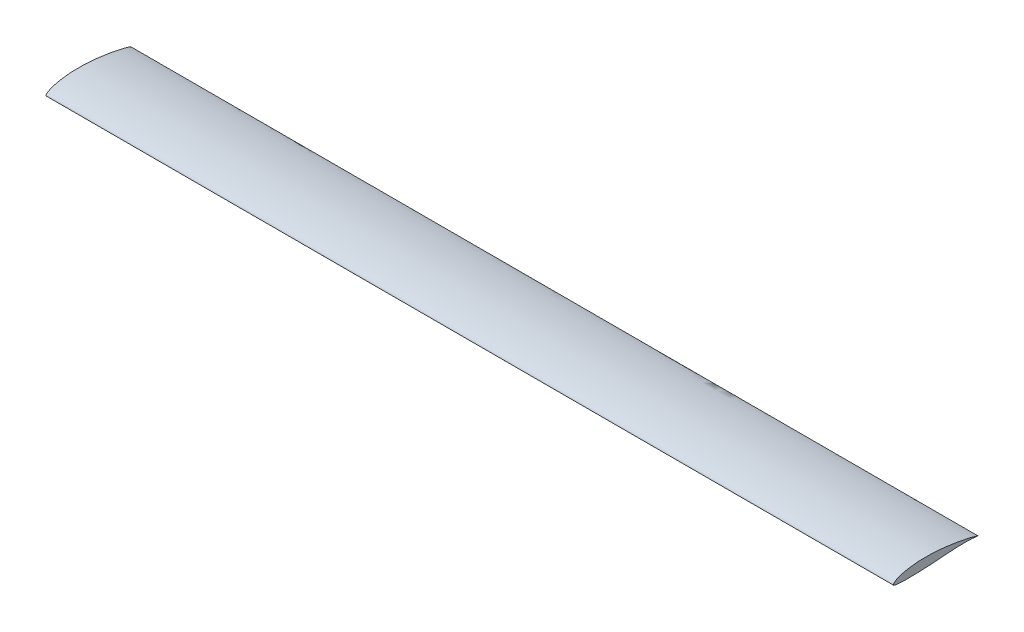
SolidWorks part; units mm, degrees
ref_plane "Front Plane" through (0, 0, 0) normal (0, 0, 1) x (1, 0, 0)
ref_plane "Top Plane" through (0, 0, 0) normal (0, 1, 0) x (1, 0, 0)
ref_plane "Right Plane" through (0, 0, 0) normal (1, 0, 0) x (0, 0, -1)
sketch "Sketch1" plane through (0, 0, 0) normal (1, 0, 0) x (0, 0, -1)
  spline S1 degree 3 poles (9.9241, 0.0152) (10.0184, -0.0046) (9.9317, 0.0203) (9.8658, 0.0458) (9.7134, 0.0985) (9.5299, 0.1554) (9.2933, 0.2186) (9.0151, 0.2871) (8.6958, 0.361) (8.3409, 0.4377) (7.9537, 0.5135) (7.538, 0.5866) (7.0981, 0.6564) (6.6389, 0.7225) (6.166, 0.7829) (5.6847, 0.8362) (5.1999, 0.8794) (4.7163, 0.9113) (4.2379, 0.9302) (3.7689, 0.9356) (3.3129, 0.9268) (2.8736, 0.9037) (2.4545, 0.8672) (2.0589, 0.8178) (1.6903, 0.7574) (1.3517, 0.6871) (1.0463, 0.6083) (0.7764, 0.5234) (0.5447, 0.4333) (0.3522, 0.3408) (0.2014, 0.248) (0.09, 0.1572) (0.0246, 0.0757) (-0.0132, -0.0074) (0.0434, -0.0803) (0.148, -0.1147) (0.2984, -0.1544) (0.502, -0.1821) (0.7547, -0.204) (1.0555, -0.2181) (1.4013, -0.2249) (1.7884, -0.2254) (2.2125, -0.2199) (2.6689, -0.2091) (3.1519, -0.1932) (3.6558, -0.1727) (4.1753, -0.1465) (4.7067, -0.1109) (5.2471, -0.0676) (5.7926, -0.024) (6.3365, 0.0162) (6.8708, 0.0503) (7.3869, 0.0766) (7.8767, 0.0934) (8.3318, 0.1009) (8.7449, 0.0987) (9.1072, 0.0887) (9.4164, 0.0709) (9.6536, 0.0511) (9.8457, 0.0249) (9.9241, 0.0152) (10.0184, -0.0046) (9.9317, 0.0203) knots -0.015816 -0.00705 -0.001765 0 0.001702 0.006531 0.013928 0.023589 0.035532 0.049689 0.065834 0.083715 0.103116 0.123879 0.145814 0.168656 0.192131 0.215962 0.239897 0.263729 0.287269 0.310326 0.332738 0.354358 0.375036 0.394629 0.412991 0.429987 0.445487 0.459385 0.471589 0.482045 0.490732 0.497663 0.502884 0.506484 0.509678 0.514915 0.522533 0.532594 0.545062 0.559872 0.576884 0.595938 0.616823 0.639301 0.6631 0.687932 0.713498 0.739627 0.76629 0.79326 0.820149 0.846538 0.872019 0.896182 0.918637 0.938996 0.95692 0.972085 0.984184 0.99295 0.998235 1 1.001702 1.006531 1.013928 only from (10, 0) to (10, 0)
extrude "Boss-Extrude1" add sketch "Sketch1" along normal blind 100
